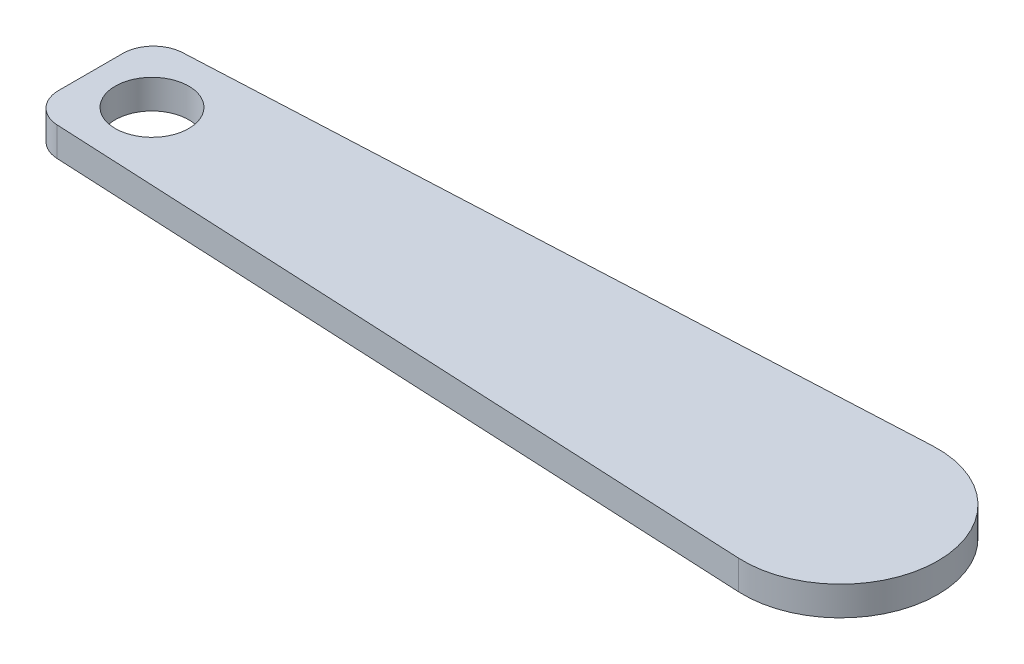
SolidWorks part; units mm, degrees
ref_plane "Front Plane" through (0, 0, 0) normal (0, 0, 1) x (1, 0, 0)
ref_plane "Top Plane" through (0, 0, 0) normal (0, 1, 0) x (1, 0, 0)
ref_plane "Right Plane" through (0, 0, 0) normal (1, 0, 0) x (0, 0, -1)
sketch "Sketch2" plane through (0, 0, 0) normal (0, 1, 0) x (1, 0, 0)
  line L0 (0, 15.8934) -> (-122.3879, 10)
  line L1 (-122.3879, -10) -> (-122.3879, 10)
  line L2 (-122.3879, -10) -> (0, -15.8934)
  line L3 (-122.3879, 0) -> (0, 0) construction
  circle A0 centre (0, 0) radius 15.875
  circle A1 centre (-112.3879, 0) radius 6
  point P8 (-122.3879, 0)
  dimension "D1" = 31.75
  dimension "D3" = 122.3879
  dimension "D2" = 12
  dimension "D5" = 10
  dimension "D6" = 20
extrude "Boss-Extrude1" add sketch "Sketch2" along normal blind 4.7625
fillet "Fillet1" radius 5 2 edges at (-122.3879, 2.3813, -10) (-122.3879, 2.3813, 10)
equation "\"steeringarmlength\"=200"
equation "\"mountingholespacing\"=15"
